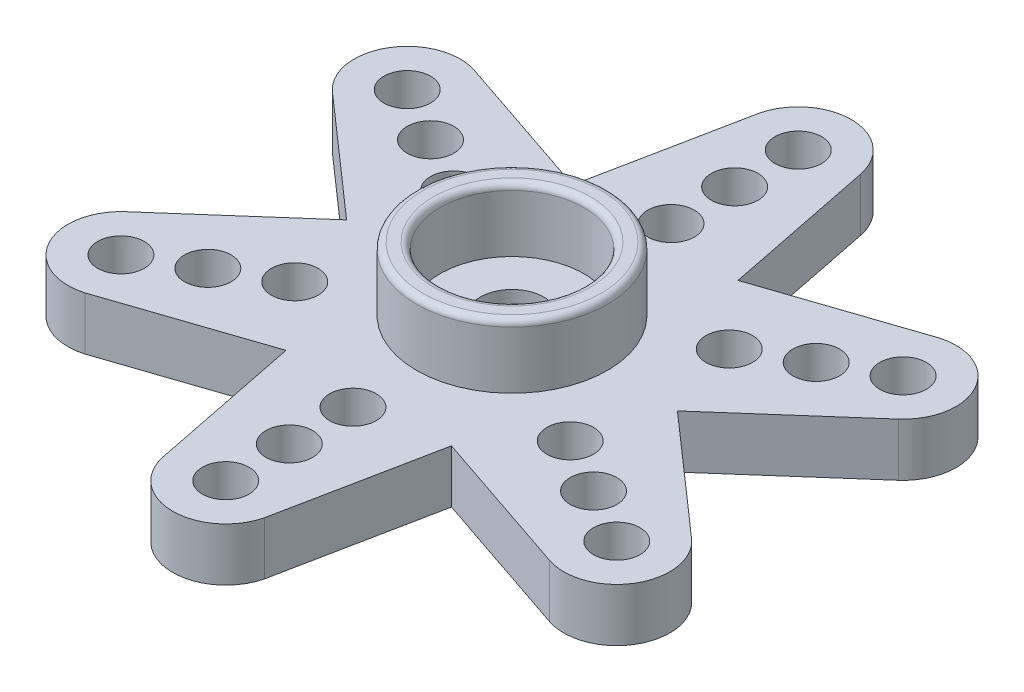
SolidWorks part; units mm, degrees
ref_plane "Alzado" through (0, 0, 0) normal (0, 0, 1) x (1, 0, 0)
ref_plane "Planta" through (0, 0, 0) normal (0, 1, 0) x (1, 0, 0)
ref_plane "Vista lateral" through (0, 0, 0) normal (1, 0, 0) x (0, 0, -1)
sketch "Croquis1" plane through (0, 0, 0) normal (0, 1, 0) x (1, 0, 0)
  line L0 (3.9, -6.755) -> (-3.9, -6.755) construction
  line L1 (0, 0) -> (0, -16) construction
  line L2 (-3.9, -6.755) -> (-10.9949, -9.151)
  line L3 (-13.342, -4.8725) -> (-7.8, 0)
  line L4 (-7.8, 0) -> (-13.4225, 4.9463)
  line L5 (-10.8907, 9.1183) -> (-3.9, 6.755)
  line L6 (-3.9, 6.755) -> (-2.4276, 14.0973)
  line L7 (2.4514, 13.9908) -> (3.9, 6.755)
  line L8 (3.9, 6.755) -> (10.9949, 9.151)
  line L9 (13.342, 4.8725) -> (7.8, 0)
  line L10 (3.9, -6.755) -> (2.4276, -14.0973)
  line L11 (7.8, 0) -> (13.4225, -4.9463)
  line L12 (-2.4514, -13.9908) -> (-3.9, -6.755)
  line L13 (10.8907, -9.1183) -> (3.9, -6.755)
  arc A0 (-13.342, -4.8725) -> (-10.9949, -9.151) centre (-11.6913, -6.75) ccw
  arc A1 (-10.8907, 9.1183) -> (-13.4225, 4.9463) centre (-11.6913, 6.75) ccw
  arc A2 (2.4514, 13.9908) -> (-2.4276, 14.0973) centre (0, 13.5) ccw
  arc A3 (13.342, 4.8725) -> (10.9949, 9.151) centre (11.6913, 6.75) ccw
  arc A4 (-2.4514, -13.9908) -> (2.4276, -14.0973) centre (0, -13.5) ccw
  arc A5 (10.8907, -9.1183) -> (13.4225, -4.9463) centre (11.6913, -6.75) ccw
  circle A6 centre (0, 0) radius 16 construction
  circle A8 centre (0, 0) radius 7.8 construction
  point P35 (0, 0)
  point P37 (0, 0)
  dimension "D1" = 32
  dimension "D5" = 5
  dimension "D2" = 15.6
extrude "Saliente-Extruir1" add sketch "Croquis1" along normal blind 2.5
sketch "Croquis2" plane through (0, 2.5, 0) normal (0, 1, 0) x (1, 0, 0)
  circle A0 centre (0, 0) radius 4.5
  circle A1 centre (0, 0) radius 3.4
  dimension "D1" = 9
  dimension "D2" = 6.8
extrude "Saliente-Extruir2" add sketch "Croquis2" along normal blind 3
sketch "Croquis3" plane through (0, 0, 0) normal (0, -1, 0) x (1, 0, 0)
  circle A0 centre (0, 0) radius 1.5
  dimension "D1" = 3
extrude "Cortar-Extruir1" cut sketch "Croquis3" against normal up to next
sketch "Croquis4" plane through (0, 0, 0) normal (0, -1, 0) x (1, 0, 0)
  circle A0 centre (0, 0) radius 2.8
  dimension "D1" = 5.6
extrude "Cortar-Extruir2" cut sketch "Croquis4" against normal offset from surface (1 mm away) 1.5 up to face at (0, 2.5, 1.5)
sketch "Croquis5" plane through (0, 0, 0) normal (0, -1, 0) x (1, 0, 0)
  circle A0 centre (0, 0) radius 4.5
  circle A1 centre (0, 0) radius 3.5
  dimension "D1" = 9
  dimension "D2" = 7
extrude "Cortar-Extruir3" cut sketch "Croquis5" against normal blind 0.5
fillet "Redondeo1" radius 0.3 5 edges at (0, 0, -4.5) (0, 0, -2.8) (0, 0, -3.5) (0, 5.5, 3.4) (0, 5.5, 4.5)
sketch "Croquis6" plane through (0, 0, 0) normal (0, -1, 0) x (1, 0, 0)
  line L0 (0, 0) -> (0, -16.5) construction
  circle A0 centre (0, 0) radius 10.5 construction
  circle A1 centre (0, 0) radius 13.5 construction
  circle A3 centre (0, 0) radius 7.5 construction
  circle A5 centre (0, -13.5) radius 1.1
  circle A6 centre (0, -10.5) radius 1.1
  circle A7 centre (0, -7.5) radius 1.1
  dimension "D2" = 27
  dimension "D3" = 21
  dimension "D4" = 15
extrude "Cortar-Extruir4" cut sketch "Croquis6" against normal up to next (2.5 mm away)
pattern_circular "MatrizC1" count 6 over 360 about axis through (0, 0, 0) along (0, 1, 0) of "Cortar-Extruir4"
